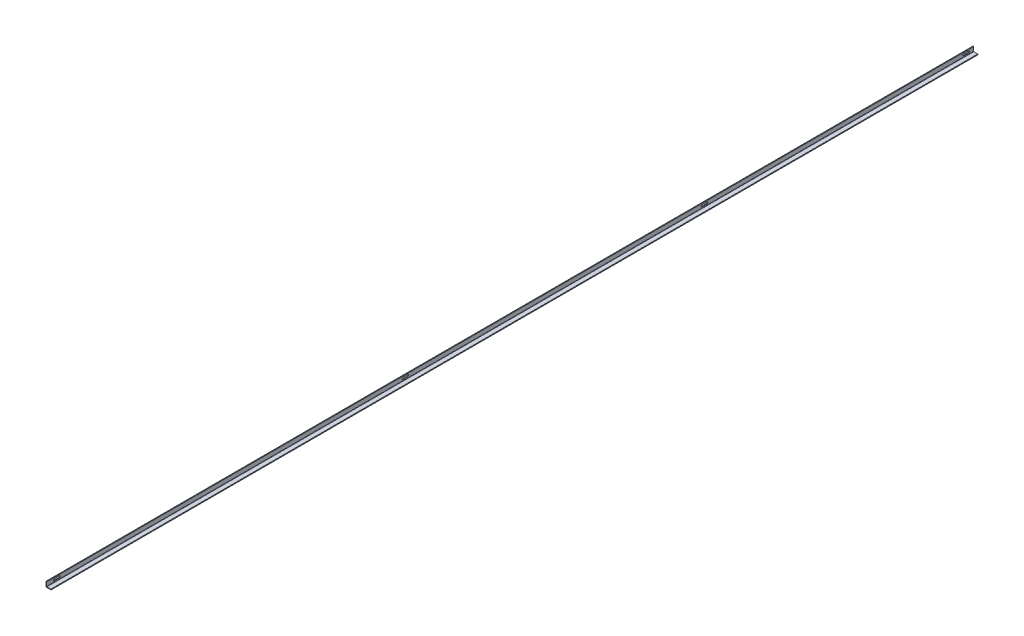
SolidWorks part; units mm, degrees
ref_plane "Front" through (0, 0, 0) normal (0, 0, 1) x (1, 0, 0)
ref_plane "Top" through (0, 0, 0) normal (0, 1, 0) x (1, 0, 0)
ref_plane "Side" through (0, 0, 0) normal (1, 0, 0) x (0, 0, -1)
sketch "Sketch1" plane through (0, 0, 0) normal (0, 0, 1) x (1, 0, 0)
  line L0 (0, 0) -> (25.4, 0)
  line L1 (0, 0) -> (0, 25.4)
  dimension "D1" = 25.4
  dimension "D2" = 25.4
extrude "Extrude-Thin1" add sketch "Sketch1" along normal blind 4660.9 thin thin type one direction wall 3.175
fillet "Fillet1" radius 1.5875 3 edges at (25.4, 3.175, 2330.45) (3.175, 3.175, 2330.45) (3.175, 25.4, 2330.45)
sketch "SlotSketch" plane through (3.175, 23.6359, 4673.5608) normal (1, 0, 0) x (0, 1, 0)
  line L0 (-9.3484, -4622.7608) -> (-9.3484, -4648.1608) construction
  line L1 (-4.9923, -4635.4608) -> (-13.7045, -4635.4608) construction
  line L2 (-4.9923, -4622.7608) -> (-4.9923, -4648.1608)
  line L3 (-13.7045, -4648.1608) -> (-13.7045, -4622.7608)
  line L5 (1.7641, -12.6608) -> (1.7641, -4673.5608) construction
  line L6 (-23.6359, -4673.5608) -> (1.7641, -4673.5608) construction
  line L7 (-23.6359, -12.6608) -> (-23.6359, -4673.5608) construction
  arc A0 (-4.9923, -4648.1608) -> (-13.7045, -4648.1608) centre (-9.3484, -4648.1608) cw
  arc A1 (-4.9923, -4622.7608) -> (-13.7045, -4622.7608) centre (-9.3484, -4622.7608) ccw
  point P12 (-9.3484, -4635.4608)
  dimension "D1" = 38.1
  dimension "Length" = 25.4
  dimension "D2" = 14.2875
  dimension "Width" = 8.7122
extrude "Slot" cut sketch "SlotSketch" against normal through all
other "straight slot<1>"
pattern_linear "Slot 2" count 2 spacing 1314.45 along (0, 0, 1) of "Slot"
pattern_linear "Slot 3" count 2 spacing 2819.4 along (0, 0, 1) of "Slot"
pattern_linear "Slot 4" count 2 spacing 4572 along (0, 0, 1) of "Slot"
sketch "Sketch2" plane through (0, 0, 0) normal (1, 0, 0) x (0, 0, -1)
  line L0 (-4622.8, 18.6436) -> (-4597.4, 18.6436) construction
  line L1 (-4660.9, 4.7625) -> (-4660.9, 23.8125) construction
  line L2 (-2870.2, 18.6436) -> (-2844.8, 18.6436) construction
  line L3 (-1365.25, 18.6436) -> (-1339.85, 18.6436) construction
  line L4 (-50.8, 18.6436) -> (-25.4, 18.6436) construction
  point P7 (-2857.5, 18.6436)
  point P8 (-1352.55, 18.6436)
  point P11 (-38.1, 18.6436)
  point P15 (-4610.1, 18.6436)
  dimension "D1" = 50.8
  dimension "D2" = 1803.4
  dimension "D3" = 3308.35
  dimension "D4" = 4622.8
